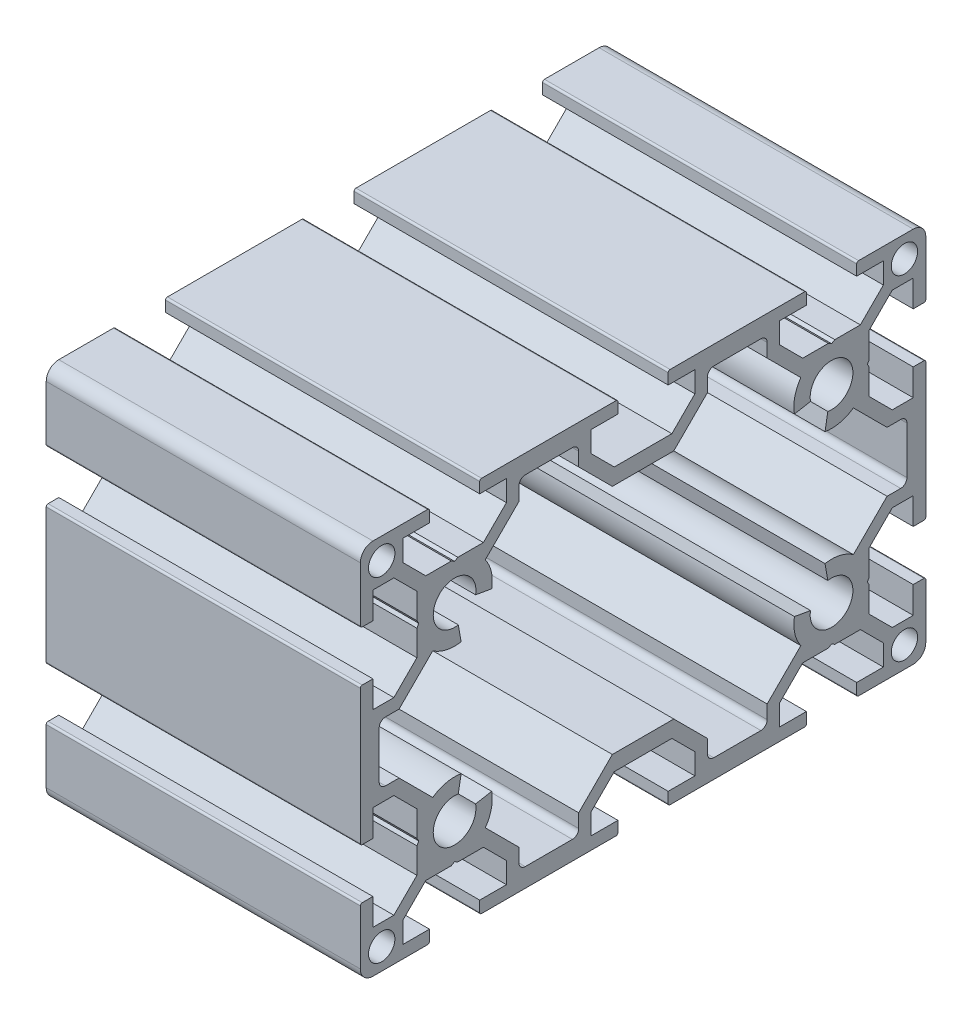
SolidWorks part; units mm, degrees
material "1060 Alloy"
ref_plane "Front Plane" through (0, 0, 0) normal (0, 0, 1) x (1, 0, 0)
ref_plane "Top Plane" through (0, 0, 0) normal (0, 1, 0) x (1, 0, 0)
ref_plane "Right Plane" through (0, 0, 0) normal (1, 0, 0) x (0, 0, -1)
sketch "Sketch1" plane through (0, 0, 0) normal (0, 0, 1) x (1, 0, 0)
  line L0 (-25, 0) -> (25, 0)
  line L1 (0, 0) -> (0, 10.9292) construction
  dimension "D1" = 50
other "Structural Member1"
ref_plane "Plane1" through (-25, 0, 0) normal (1, 0, 0) x (0, 1, 0)
sketch "Sketch11" plane through (-25, 0, 0) normal (1, 0, 0) x (0, 1, 0)
  line L0 (-30, 25.7) -> (-30, 4.3)
  line L1 (-28, 26) -> (-29.7, 26)
  line L2 (-28, 21.75) -> (-28, 26)
  line L3 (-24.6642, 21.75) -> (-28, 21.75)
  line L4 (-21, 25.4142) -> (-24.6642, 21.75)
  line L5 (-21, 29.4804) -> (-21, 25.4142)
  line L6 (-20.7, 30) -> (-21, 29.4804)
  line L7 (-21, 30.5196) -> (-20.7, 30)
  line L8 (-21, 34.5858) -> (-21, 30.5196)
  line L9 (-24.6642, 38.25) -> (-21, 34.5858)
  line L10 (-28, 38.25) -> (-24.6642, 38.25)
  line L11 (-28, 34) -> (-28, 38.25)
  line L12 (-29.7, 34) -> (-28, 34)
  line L13 (-30, 43) -> (-30, 34.3)
  line L14 (-19.3, 45) -> (-28, 45)
  line L15 (-19, 43) -> (-19, 44.7)
  line L16 (-23.25, 43) -> (-19, 43)
  line L17 (-23.25, 39.6642) -> (-23.25, 43)
  line L18 (-19.5858, 36) -> (-23.25, 39.6642)
  line L19 (-15.5196, 36) -> (-19.5858, 36)
  line L20 (-15, 35.7) -> (-15.5196, 36)
  line L21 (-14.4804, 36) -> (-15, 35.7)
  line L22 (-10.4142, 36) -> (-14.4804, 36)
  line L23 (-6.75, 39.6642) -> (-10.4142, 36)
  line L24 (-6.75, 43) -> (-6.75, 39.6642)
  line L25 (-11, 43) -> (-6.75, 43)
  line L26 (-11, 44.7) -> (-11, 43)
  line L27 (10.7, 45) -> (-10.7, 45)
  line L28 (11, 43) -> (11, 44.7)
  line L29 (6.75, 43) -> (11, 43)
  line L30 (6.75, 39.6642) -> (6.75, 43)
  line L31 (10.4142, 36) -> (6.75, 39.6642)
  line L32 (14.4804, 36) -> (10.4142, 36)
  line L33 (15, 35.7) -> (14.4804, 36)
  line L34 (15.5196, 36) -> (15, 35.7)
  line L35 (19.5858, 36) -> (15.5196, 36)
  line L36 (23.25, 39.6642) -> (19.5858, 36)
  line L37 (23.25, 43) -> (23.25, 39.6642)
  line L38 (19, 43) -> (23.25, 43)
  line L39 (19, 44.7) -> (19, 43)
  line L40 (28, 45) -> (19.3, 45)
  line L41 (30, 34.3) -> (30, 43)
  line L42 (28, 34) -> (29.7, 34)
  line L43 (28, 38.25) -> (28, 34)
  line L44 (24.6642, 38.25) -> (28, 38.25)
  line L45 (21, 34.5858) -> (24.6642, 38.25)
  line L46 (21, 30.5196) -> (21, 34.5858)
  line L47 (20.7, 30) -> (21, 30.5196)
  line L48 (21, 29.4804) -> (20.7, 30)
  line L49 (21, 25.4142) -> (21, 29.4804)
  line L50 (24.6642, 21.75) -> (21, 25.4142)
  line L51 (28, 21.75) -> (24.6642, 21.75)
  line L52 (28, 26) -> (28, 21.75)
  line L53 (29.7, 26) -> (28, 26)
  line L54 (30, 4.3) -> (30, 25.7)
  line L55 (28, 4) -> (29.7, 4)
  line L56 (28, 8.25) -> (28, 4)
  line L57 (24.6642, 8.25) -> (28, 8.25)
  line L58 (21, 4.5858) -> (24.6642, 8.25)
  line L59 (21, -4.5858) -> (21, 4.5858)
  line L60 (24.6642, -8.25) -> (21, -4.5858)
  line L61 (28, -8.25) -> (24.6642, -8.25)
  line L62 (28, -4) -> (28, -8.25)
  line L63 (29.7, -4) -> (28, -4)
  line L64 (30, -25.7) -> (30, -4.3)
  line L65 (28, -26) -> (29.7, -26)
  line L66 (28, -21.75) -> (28, -26)
  line L67 (24.6642, -21.75) -> (28, -21.75)
  line L68 (21, -25.4142) -> (24.6642, -21.75)
  line L69 (21, -29.4804) -> (21, -25.4142)
  line L70 (20.7, -30) -> (21, -29.4804)
  line L71 (21, -30.5196) -> (20.7, -30)
  line L72 (21, -34.5858) -> (21, -30.5196)
  line L73 (24.6642, -38.25) -> (21, -34.5858)
  line L74 (28, -38.25) -> (24.6642, -38.25)
  line L75 (28, -34) -> (28, -38.25)
  line L76 (29.7, -34) -> (28, -34)
  line L77 (30, -43) -> (30, -34.3)
  line L78 (19.3, -45) -> (28, -45)
  line L79 (19, -43) -> (19, -44.7)
  line L80 (23.25, -43) -> (19, -43)
  line L81 (23.25, -39.6642) -> (23.25, -43)
  line L82 (19.5858, -36) -> (23.25, -39.6642)
  line L83 (15.5196, -36) -> (19.5858, -36)
  line L84 (15, -35.7) -> (15.5196, -36)
  line L85 (14.4804, -36) -> (15, -35.7)
  line L86 (10.4142, -36) -> (14.4804, -36)
  line L87 (6.75, -39.6642) -> (10.4142, -36)
  line L88 (6.75, -43) -> (6.75, -39.6642)
  line L89 (11, -43) -> (6.75, -43)
  line L90 (11, -44.7) -> (11, -43)
  line L91 (-10.7, -45) -> (10.7, -45)
  line L92 (-11, -43) -> (-11, -44.7)
  line L93 (-6.75, -43) -> (-11, -43)
  line L94 (-6.75, -39.6642) -> (-6.75, -43)
  line L95 (-10.4142, -36) -> (-6.75, -39.6642)
  line L96 (-14.4804, -36) -> (-10.4142, -36)
  line L97 (-15, -35.7) -> (-14.4804, -36)
  line L98 (-15.5196, -36) -> (-15, -35.7)
  line L99 (-19.5858, -36) -> (-15.5196, -36)
  line L100 (-23.25, -39.6642) -> (-19.5858, -36)
  line L101 (-23.25, -43) -> (-23.25, -39.6642)
  line L102 (-19, -43) -> (-23.25, -43)
  line L103 (-19, -44.7) -> (-19, -43)
  line L104 (-28, -45) -> (-19.3, -45)
  line L105 (-30, -34.3) -> (-30, -43)
  line L106 (-28, -34) -> (-29.7, -34)
  line L107 (-28, -38.25) -> (-28, -34)
  line L108 (-24.6642, -38.25) -> (-28, -38.25)
  line L109 (-21, -34.5858) -> (-24.6642, -38.25)
  line L110 (-21, -30.5196) -> (-21, -34.5858)
  line L111 (-20.7, -30) -> (-21, -30.5196)
  line L112 (-21, -29.4804) -> (-20.7, -30)
  line L113 (-21, -25.4142) -> (-21, -29.4804)
  line L114 (-24.6642, -21.75) -> (-21, -25.4142)
  line L115 (-28, -21.75) -> (-24.6642, -21.75)
  line L116 (-28, -26) -> (-28, -21.75)
  line L117 (-29.7, -26) -> (-28, -26)
  line L118 (-30, -4.3) -> (-30, -25.7)
  line L119 (-28, -4) -> (-29.7, -4)
  line L120 (-28, -8.25) -> (-28, -4)
  line L121 (-24.6642, -8.25) -> (-28, -8.25)
  line L122 (-21, -4.5858) -> (-24.6642, -8.25)
  line L123 (-21, 4.5858) -> (-21, -4.5858)
  line L124 (-24.6642, 8.25) -> (-21, 4.5858)
  line L125 (-28, 8.25) -> (-24.6642, 8.25)
  line L126 (-28, 4) -> (-28, 8.25)
  line L127 (-29.7, 4) -> (-28, 4)
  line L128 (-27, 18.75) -> (-27, 11.25)
  line L129 (-26, 10.25) -> (-23.8358, 10.25)
  line L130 (-23.8358, 10.25) -> (-18.4762, 4.8904)
  line L131 (-18.4762, 4.8904) -> (-18.4762, -4.8904)
  line L132 (-18.4762, -4.8904) -> (-23.8358, -10.25)
  line L133 (-23.8358, -10.25) -> (-26, -10.25)
  line L134 (-27, -11.25) -> (-27, -18.75)
  line L135 (-26, -19.75) -> (-23.8358, -19.75)
  line L136 (-23.8358, -19.75) -> (-18.4762, -25.1096)
  line L137 (-13.9581, -24.0912) -> (-14.4096, -26.6517)
  line L138 (-11.6517, -29.4096) -> (-9.0912, -28.9581)
  line L139 (-10.1096, -33.4762) -> (-4.75, -38.8358)
  line L140 (-4.75, -38.8358) -> (-4.75, -41)
  line L141 (-3.75, -42) -> (3.75, -42)
  line L142 (4.75, -41) -> (4.75, -38.8358)
  line L143 (4.75, -38.8358) -> (10.1096, -33.4762)
  line L144 (9.0912, -28.9581) -> (11.6517, -29.4096)
  line L145 (14.4096, -26.6517) -> (13.9581, -24.0912)
  line L146 (18.4762, -25.1096) -> (23.8358, -19.75)
  line L147 (23.8358, -19.75) -> (26, -19.75)
  line L148 (27, -18.75) -> (27, -11.25)
  line L149 (26, -10.25) -> (23.8358, -10.25)
  line L150 (23.8358, -10.25) -> (18.4762, -4.8904)
  line L151 (18.4762, -4.8904) -> (18.4762, 4.8904)
  line L152 (18.4762, 4.8904) -> (23.8358, 10.25)
  line L153 (23.8358, 10.25) -> (26, 10.25)
  line L154 (27, 11.25) -> (27, 18.75)
  line L155 (26, 19.75) -> (23.8358, 19.75)
  line L156 (23.8358, 19.75) -> (18.4762, 25.1096)
  line L157 (13.9581, 24.0912) -> (14.4096, 26.6517)
  line L158 (11.6517, 29.4096) -> (9.0912, 28.9581)
  line L159 (10.1096, 33.4762) -> (4.75, 38.8358)
  line L160 (4.75, 38.8358) -> (4.75, 41)
  line L161 (3.75, 42) -> (-3.75, 42)
  line L162 (-4.75, 41) -> (-4.75, 38.8358)
  line L163 (-4.75, 38.8358) -> (-10.1096, 33.4762)
  line L164 (-9.0912, 28.9581) -> (-11.6517, 29.4096)
  line L165 (-14.4096, 26.6517) -> (-13.9581, 24.0912)
  line L166 (-18.4762, 25.1096) -> (-23.8358, 19.75)
  line L167 (-23.8358, 19.75) -> (-26, 19.75)
  line L168 (23.4183, -41.6) -> (29.7817, -41.6) construction
  line L169 (26.6, -44.7817) -> (26.6, -38.4183) construction
  line L170 (23.4183, 41.6) -> (29.7817, 41.6) construction
  line L171 (26.6, 38.4183) -> (26.6, 44.7817) construction
  line L172 (-29.7817, -41.6) -> (-23.4183, -41.6) construction
  line L173 (-26.6, -44.7817) -> (-26.6, -38.4183) construction
  line L174 (-29.7817, 41.6) -> (-23.4183, 41.6) construction
  line L175 (-26.6, 38.4183) -> (-26.6, 44.7817) construction
  line L176 (-31.0817, 25.7) -> (-28.3183, 25.7) construction
  line L177 (-29.7, 24.3183) -> (-29.7, 27.0817) construction
  line L178 (-31.0817, 34.3) -> (-28.3183, 34.3) construction
  line L179 (-29.7, 32.9183) -> (-29.7, 35.6817) construction
  line L180 (-31.0817, 43) -> (-24.9183, 43) construction
  line L181 (-28, 39.9183) -> (-28, 46.0817) construction
  line L182 (-12.0817, 44.7) -> (-9.3183, 44.7) construction
  line L183 (-10.7, 43.3183) -> (-10.7, 46.0817) construction
  line L184 (9.3183, 44.7) -> (12.0817, 44.7) construction
  line L185 (10.7, 43.3183) -> (10.7, 46.0817) construction
  line L186 (17.9183, 44.7) -> (20.6817, 44.7) construction
  line L187 (19.3, 43.3183) -> (19.3, 46.0817) construction
  line L188 (28.3183, 34.3) -> (31.0817, 34.3) construction
  line L189 (29.7, 32.9183) -> (29.7, 35.6817) construction
  line L190 (28.3183, 25.7) -> (31.0817, 25.7) construction
  line L191 (29.7, 24.3183) -> (29.7, 27.0817) construction
  line L192 (28.3183, -25.7) -> (31.0817, -25.7) construction
  line L193 (29.7, -27.0817) -> (29.7, -24.3183) construction
  line L194 (28.3183, -34.3) -> (31.0817, -34.3) construction
  line L195 (29.7, -35.6817) -> (29.7, -32.9183) construction
  line L196 (24.9183, -43) -> (31.0817, -43) construction
  line L197 (28, -46.0817) -> (28, -39.9183) construction
  line L198 (17.9183, -44.7) -> (20.6817, -44.7) construction
  line L199 (19.3, -46.0817) -> (19.3, -43.3183) construction
  line L200 (9.3183, -44.7) -> (12.0817, -44.7) construction
  line L201 (10.7, -46.0817) -> (10.7, -43.3183) construction
  line L202 (-12.0817, -44.7) -> (-9.3183, -44.7) construction
  line L203 (-10.7, -46.0817) -> (-10.7, -43.3183) construction
  line L204 (-20.6817, -44.7) -> (-17.9183, -44.7) construction
  line L205 (-19.3, -46.0817) -> (-19.3, -43.3183) construction
  line L206 (-31.0817, -34.3) -> (-28.3183, -34.3) construction
  line L207 (-29.7, -35.6817) -> (-29.7, -32.9183) construction
  line L208 (-31.0817, -25.7) -> (-28.3183, -25.7) construction
  line L209 (-29.7, -27.0817) -> (-29.7, -24.3183) construction
  line L210 (-28.0817, 11.25) -> (-23.9183, 11.25) construction
  line L211 (-26, 9.1683) -> (-26, 13.3317) construction
  line L212 (-28.0817, -11.25) -> (-23.9183, -11.25) construction
  line L213 (-26, -13.3317) -> (-26, -9.1683) construction
  line L214 (-28.0817, -18.75) -> (-23.9183, -18.75) construction
  line L215 (-26, -20.8317) -> (-26, -16.6683) construction
  line L216 (-22.0817, -30) -> (-7.9183, -30) construction
  line L217 (-15, -37.0817) -> (-15, -22.9183) construction
  line L218 (7.9183, -30) -> (22.0817, -30) construction
  line L219 (15, -37.0817) -> (15, -22.9183) construction
  line L220 (23.9183, -11.25) -> (28.0817, -11.25) construction
  line L221 (26, -13.3317) -> (26, -9.1683) construction
  line L222 (23.9183, 11.25) -> (28.0817, 11.25) construction
  line L223 (26, 9.1683) -> (26, 13.3317) construction
  line L224 (7.9183, 30) -> (22.0817, 30) construction
  line L225 (15, 22.9183) -> (15, 37.0817) construction
  line L226 (-22.0817, 30) -> (-7.9183, 30) construction
  line L227 (-15, 22.9183) -> (-15, 37.0817) construction
  line L228 (-28.0817, 18.75) -> (-23.9183, 18.75) construction
  line L229 (-26, 16.6683) -> (-26, 20.8317) construction
  arc A0 (-30, 4.3) -> (-29.7, 4) centre (-29.7, 4.3) ccw
  arc A1 (-29.7, 26) -> (-30, 25.7) centre (-29.7, 25.7) ccw
  arc A2 (-30, 34.3) -> (-29.7, 34) centre (-29.7, 34.3) ccw
  arc A3 (-28, 45) -> (-30, 43) centre (-28, 43) ccw
  arc A4 (-19, 44.7) -> (-19.3, 45) centre (-19.3, 44.7) ccw
  arc A5 (-10.7, 45) -> (-11, 44.7) centre (-10.7, 44.7) ccw
  arc A6 (11, 44.7) -> (10.7, 45) centre (10.7, 44.7) ccw
  arc A7 (19.3, 45) -> (19, 44.7) centre (19.3, 44.7) ccw
  arc A8 (30, 43) -> (28, 45) centre (28, 43) ccw
  arc A9 (29.7, 34) -> (30, 34.3) centre (29.7, 34.3) ccw
  arc A10 (30, 25.7) -> (29.7, 26) centre (29.7, 25.7) ccw
  arc A11 (29.7, 4) -> (30, 4.3) centre (29.7, 4.3) ccw
  arc A12 (30, -4.3) -> (29.7, -4) centre (29.7, -4.3) ccw
  arc A13 (29.7, -26) -> (30, -25.7) centre (29.7, -25.7) ccw
  arc A14 (30, -34.3) -> (29.7, -34) centre (29.7, -34.3) ccw
  arc A15 (28, -45) -> (30, -43) centre (28, -43) ccw
  arc A16 (19, -44.7) -> (19.3, -45) centre (19.3, -44.7) ccw
  arc A17 (10.7, -45) -> (11, -44.7) centre (10.7, -44.7) ccw
  arc A18 (-11, -44.7) -> (-10.7, -45) centre (-10.7, -44.7) ccw
  arc A19 (-19.3, -45) -> (-19, -44.7) centre (-19.3, -44.7) ccw
  arc A20 (-30, -43) -> (-28, -45) centre (-28, -43) ccw
  arc A21 (-29.7, -34) -> (-30, -34.3) centre (-29.7, -34.3) ccw
  arc A22 (-30, -25.7) -> (-29.7, -26) centre (-29.7, -25.7) ccw
  arc A23 (-29.7, -4) -> (-30, -4.3) centre (-29.7, -4.3) ccw
  circle A24 centre (26.6, -41.6) radius 2.1
  circle A25 centre (26.6, 41.6) radius 2.1
  arc A26 (-27, 11.25) -> (-26, 10.25) centre (-26, 11.25) ccw
  arc A27 (-26, -10.25) -> (-27, -11.25) centre (-26, -11.25) ccw
  arc A28 (-27, -18.75) -> (-26, -19.75) centre (-26, -18.75) ccw
  arc A29 (-13.9581, -24.0912) -> (-18.4762, -25.1096) centre (-15, -30) ccw
  arc A30 (-14.4096, -26.6517) -> (-11.6517, -29.4096) centre (-15, -30) ccw
  arc A31 (-10.1096, -33.4762) -> (-9.0912, -28.9581) centre (-15, -30) ccw
  arc A32 (-4.75, -41) -> (-3.75, -42) centre (-3.75, -41) ccw
  arc A33 (3.75, -42) -> (4.75, -41) centre (3.75, -41) ccw
  arc A34 (9.0912, -28.9581) -> (10.1096, -33.4762) centre (15, -30) ccw
  arc A35 (11.6517, -29.4096) -> (14.4096, -26.6517) centre (15, -30) ccw
  arc A36 (18.4762, -25.1096) -> (13.9581, -24.0912) centre (15, -30) ccw
  arc A37 (26, -19.75) -> (27, -18.75) centre (26, -18.75) ccw
  arc A38 (27, -11.25) -> (26, -10.25) centre (26, -11.25) ccw
  arc A39 (26, 10.25) -> (27, 11.25) centre (26, 11.25) ccw
  arc A40 (27, 18.75) -> (26, 19.75) centre (26, 18.75) ccw
  arc A41 (13.9581, 24.0912) -> (18.4762, 25.1096) centre (15, 30) ccw
  arc A42 (14.4096, 26.6517) -> (11.6517, 29.4096) centre (15, 30) ccw
  arc A43 (10.1096, 33.4762) -> (9.0912, 28.9581) centre (15, 30) ccw
  arc A44 (4.75, 41) -> (3.75, 42) centre (3.75, 41) ccw
  arc A45 (-3.75, 42) -> (-4.75, 41) centre (-3.75, 41) ccw
  arc A46 (-9.0912, 28.9581) -> (-10.1096, 33.4762) centre (-15, 30) ccw
  arc A47 (-11.6517, 29.4096) -> (-14.4096, 26.6517) centre (-15, 30) ccw
  arc A48 (-18.4762, 25.1096) -> (-13.9581, 24.0912) centre (-15, 30) ccw
  arc A49 (-26, 19.75) -> (-27, 18.75) centre (-26, 18.75) ccw
  circle A50 centre (-26.6, -41.6) radius 2.1
  circle A51 centre (-26.6, 41.6) radius 2.1
  point P0 (0, 0)
